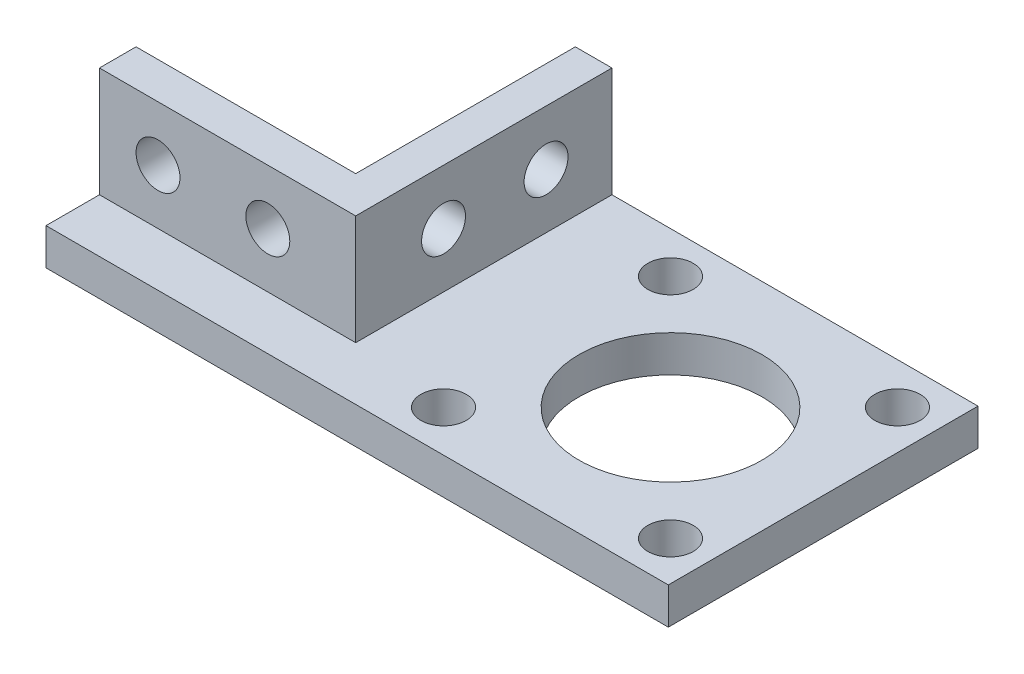
SolidWorks part; units mm, degrees
ref_plane "Front Plane" through (0, 0, 0) normal (0, 0, 1) x (1, 0, 0)
ref_plane "Top Plane" through (0, 0, 0) normal (0, 1, 0) x (1, 0, 0)
ref_plane "Right Plane" through (0, 0, 0) normal (1, 0, 0) x (0, 0, -1)
sketch "Esboço1" plane through (0, 0, 0) normal (0, 0, 1) x (1, 0, 0)
  line L1 (-64.2052, -275) -> (-94.2052, -275) construction
  line L2 (-64.2052, -550) -> (-64.2052, 0) construction
  line L3 (-94.2052, -550) -> (-94.2052, 0) construction
  line L5 (-94.2052, -275) -> (-59.2052, -275)
  line L6 (-94.2052, -275) -> (-94.2052, -255)
  line L7 (-94.2052, -255) -> (-59.2052, -255)
  line L8 (-59.2052, -275) -> (-59.2052, -255)
  dimension "D1" = 35
  dimension "D2" = 20
extrude "Ressalto-extrusão1" add sketch "Esboço1" along normal blind 5
sketch "Esboço2" plane through (0, 0, 0) normal (0, 0, -1) x (-1, 0, 0)
  line L0 (64.2052, -550) -> (64.2052, 0) construction
  line L1 (64.2052, -275) -> (59.2052, -275)
  line L2 (64.2052, -275) -> (64.2052, -255)
  line L3 (64.2052, -255) -> (59.2052, -255)
  line L4 (59.2052, -275) -> (59.2052, -255)
extrude "Ressalto-extrusão2" add sketch "Esboço2" along normal up to vertex (30 mm away)
sketch "Esboço4" plane through (-59.2052, 0, 0) normal (1, 0, 0) x (0, 0, -1)
  line L0 (-12.3, -258) -> (-12.3, -269) construction
  line L1 (30, -275) -> (-12.3, -275)
  line L2 (30, -275) -> (30, -270)
  line L3 (30, -270) -> (-12.3, -270)
  line L4 (-12.3, -275) -> (-12.3, -270)
  dimension "D1" = 5
extrude "Ressalto-extrusão3" add sketch "Esboço4" along normal blind 50
sketch "Esboço5" plane through (-59.2052, 0, 0) normal (-1, 0, 0) x (0, 0, 1)
  line L8 (5, -270) -> (5, -275)
  line L9 (5, -275) -> (12.3, -275)
  line L10 (12.3, -275) -> (12.3, -270)
  line L11 (12.3, -270) -> (5, -270)
  line L12 (5, -270) -> (5, -275)
  line L13 (5, -275) -> (12.3, -275)
  line L14 (12.3, -275) -> (12.3, -270)
  line L15 (12.3, -270) -> (5, -270)
  dimension "D1" = 0
extrude "Ressalto-extrusão4" add sketch "Esboço5" along normal up to vertex (35 mm away) up to point (-94.2052, -255, 5)
sketch "Esboço6" plane through (0, -275, 0) normal (0, -1, 0) x (1, 0, 0)
  circle A2 centre (-14.5552, 6.65) radius 3.1
  circle A3 centre (-14.5552, 6.65) radius 3.1
  circle A4 centre (-30.0552, -8.85) radius 12.5
  circle A5 centre (-45.5552, -24.35) radius 3.1
  circle A6 centre (-45.5552, -24.35) radius 3.1
  circle A7 centre (-30.0552, -8.85) radius 12.5
  circle A8 centre (-45.5552, 6.65) radius 3.1
  circle A9 centre (-45.5552, 6.65) radius 3.1
  circle A11 centre (-14.5552, -24.35) radius 3.1
  circle A12 centre (-14.5552, -24.35) radius 3.1
  dimension "D1" = 0
  dimension "D2" = 0
  dimension "D3" = 0
  dimension "D4" = 0
  dimension "D5" = 10
extrude "Corte-extrusão1" cut sketch "Esboço6" against normal blind 39
sketch "Esboço7" plane through (-59.2052, 0, 0) normal (1, 0, 0) x (0, 0, -1)
  line L0 (30, -262.5) -> (-5, -262.5) construction
  line L1 (30, -255) -> (30, -270) construction
  line L2 (-5, -270) -> (-5, -255) construction
  circle A0 centre (21, -262.5) radius 3
  circle A1 centre (7, -262.5) radius 3
  dimension "D1" = 6
  dimension "D2" = 12
  dimension "D3" = 9
extrude "Corte-extrusão2" cut sketch "Esboço7" against normal through all
sketch "Esboço8" plane through (0, 0, 5) normal (0, 0, 1) x (1, 0, 0)
  line L0 (-59.2052, -262.5) -> (-94.2052, -262.5) construction
  line L1 (-59.2052, -270) -> (-59.2052, -255) construction
  line L2 (-94.2052, -255) -> (-94.2052, -270) construction
  circle A0 centre (-71.2052, -262.5) radius 3
  circle A1 centre (-86.2052, -262.5) radius 3
  dimension "D1" = 6
  dimension "D2" = 6
  dimension "D3" = 12
  dimension "D4" = 8
extrude "Corte-extrusão3" cut sketch "Esboço8" against normal blind 10
